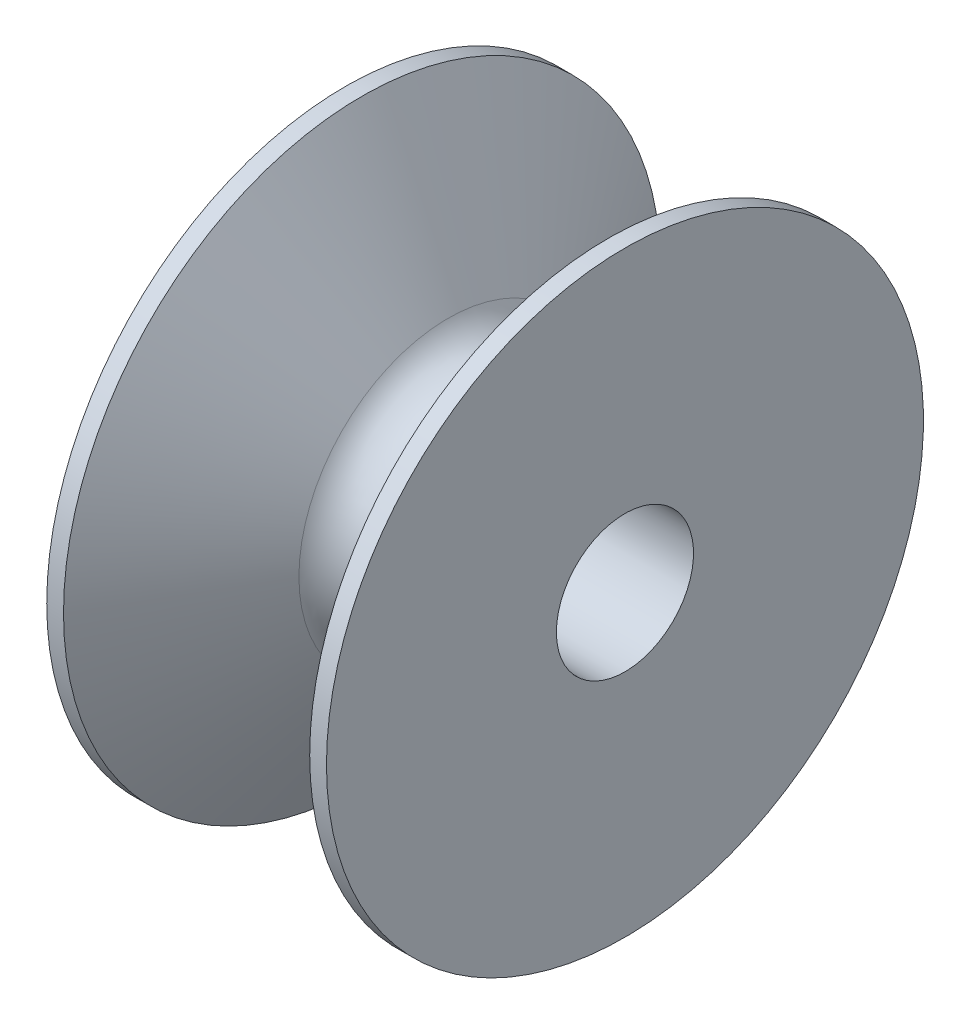
SolidWorks part; units mm, degrees
material "PET"
ref_plane "Front" through (0, 0, 0) normal (0, 0, 1) x (1, 0, 0)
ref_plane "Top" through (0, 0, 0) normal (0, 1, 0) x (1, 0, 0)
ref_plane "Right" through (0, 0, 0) normal (1, 0, 0) x (0, 0, -1)
sketch "Sketch1" plane through (0, 0, 0) normal (0, 0, 1) x (1, 0, 0)
  line L0 (0, 2.5527) -> (10.414, 2.5527)
  line L1 (10.414, 2.5527) -> (10.414, 11.1125)
  line L2 (10.414, 11.1125) -> (9.7897, 11.1125)
  line L3 (9.7897, 11.1125) -> (6.5818, 5.5563)
  line L4 (3.8322, 5.5563) -> (0.6243, 11.1125)
  line L5 (0.6243, 11.1125) -> (0, 11.1125)
  line L6 (0, 11.1125) -> (0, 2.5527)
  line L7 (0, 0) -> (13.0175, 0) construction
  arc A0 (6.5818, 5.5563) -> (3.8322, 5.5563) centre (5.207, 6.35) cw
  point P12 (9.0551, 9.525)
  dimension "D4" = 9.525
  dimension "D6" = 3.175
  dimension "D1" = 10.414
  dimension "D2" = 5.1054
  dimension "D3" = 22.225
  dimension "D5" = 60
revolve "Revolve1" add sketch "Sketch1" angle 360 about L7
